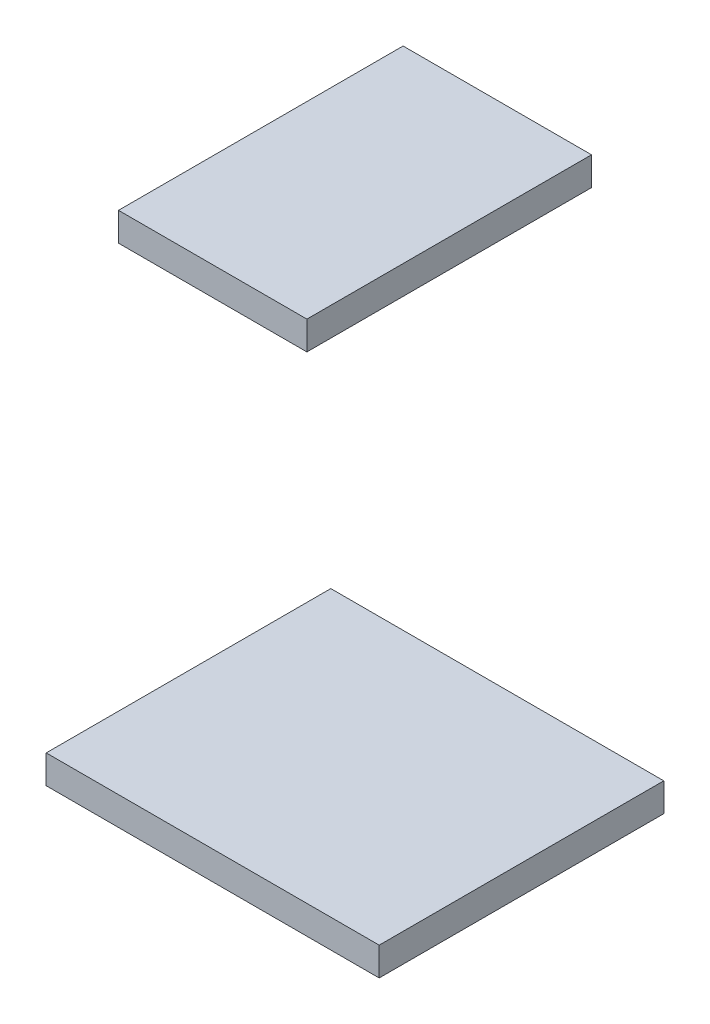
SolidWorks part; units mm, degrees
ref_plane "Ebene vorne" through (0, 0, 0) normal (0, 0, 1) x (1, 0, 0)
ref_plane "Ebene oben" through (0, 0, 0) normal (0, 1, 0) x (1, 0, 0)
ref_plane "Ebene rechts" through (0, 0, 0) normal (1, 0, 0) x (0, 0, -1)
sketch "Skizze1" plane through (0, 0, 0) normal (0, 0, 1) x (1, 0, 0)
  line L1 (102.195, -35.19) -> (90.495, -35.19)
  line L2 (102.195, -35.19) -> (102.195, -36.19)
  line L3 (102.195, -36.19) -> (90.495, -36.19)
  line L4 (90.495, -35.19) -> (90.495, -36.19)
  line L5 (99.655, -17.41) -> (93.035, -17.41)
  line L6 (99.655, -17.41) -> (99.655, -18.41)
  line L7 (99.655, -18.41) -> (93.035, -18.41)
  line L8 (93.035, -17.41) -> (93.035, -18.41)
  circle A4 centre (102.695, -35.69) radius 0.5 construction
  circle A5 centre (89.995, -35.69) radius 0.5 construction
  circle A6 centre (92.535, -17.91) radius 0.5 construction
  circle A7 centre (100.155, -17.91) radius 0.5 construction
extrude "Aufsatz-Linear austragen1" add sketch "Skizze1" along normal blind 10
